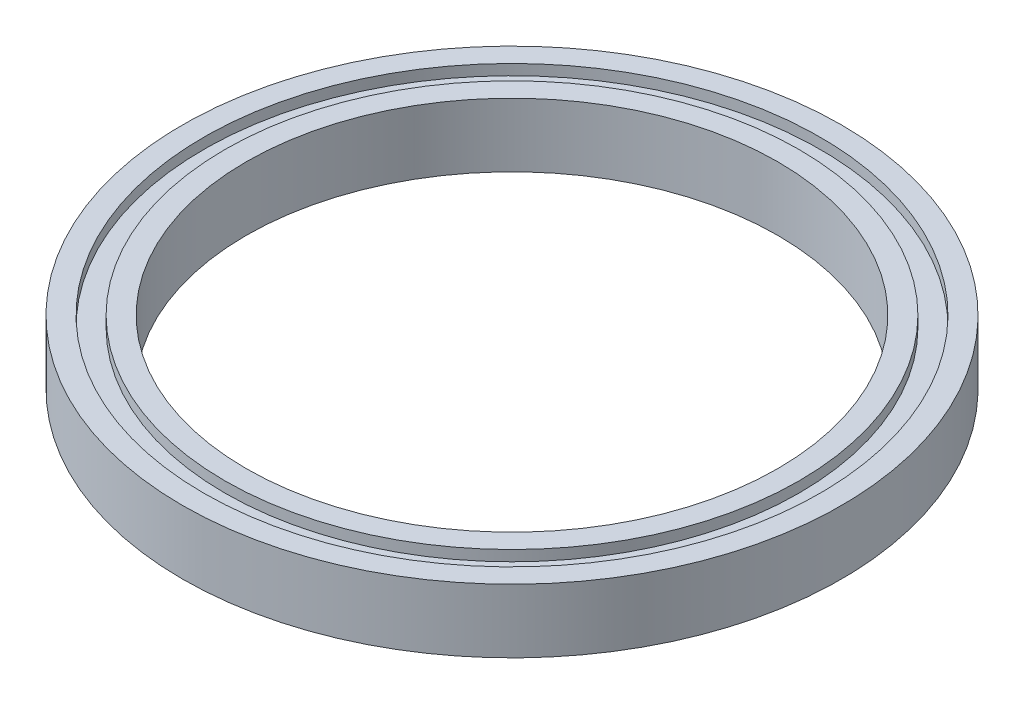
SolidWorks part; units mm, degrees
ref_plane "Front Plane" through (0, 0, 0) normal (0, 0, 1) x (1, 0, 0)
ref_plane "Top Plane" through (0, 0, 0) normal (0, 1, 0) x (1, 0, 0)
ref_plane "Right Plane" through (0, 0, 0) normal (1, 0, 0) x (0, 0, -1)
sketch "Sketch1" plane through (0, 0, 0) normal (0, 1, 0) x (1, 0, 0)
  circle A0 centre (0, 0) radius 25
  circle A1 centre (0, 0) radius 31
  dimension "D1" = 62
  dimension "D2" = 50
extrude "Boss-Extrude1" add sketch "Sketch1" along normal blind 6
sketch "Sketch2" plane through (0, 6, 0) normal (0, 1, 0) x (1, 0, 0)
  circle A2 centre (0, 0) radius 29
  circle A3 centre (0, 0) radius 29
  circle A5 centre (0, 0) radius 27
  circle A6 centre (0, 0) radius 27
  dimension "D1" = 2
  dimension "D2" = 2
extrude "Cut-Extrude1" cut sketch "Sketch2" against normal blind 1
sketch "Sketch3" plane through (0, 0, 0) normal (0, -1, 0) x (1, 0, 0)
  circle A2 centre (0, 0) radius 29
  circle A3 centre (0, 0) radius 29
  circle A5 centre (0, 0) radius 27
  circle A6 centre (0, 0) radius 27
  dimension "D1" = 2
  dimension "D2" = 2
extrude "Cut-Extrude2" cut sketch "Sketch3" against normal blind 1
